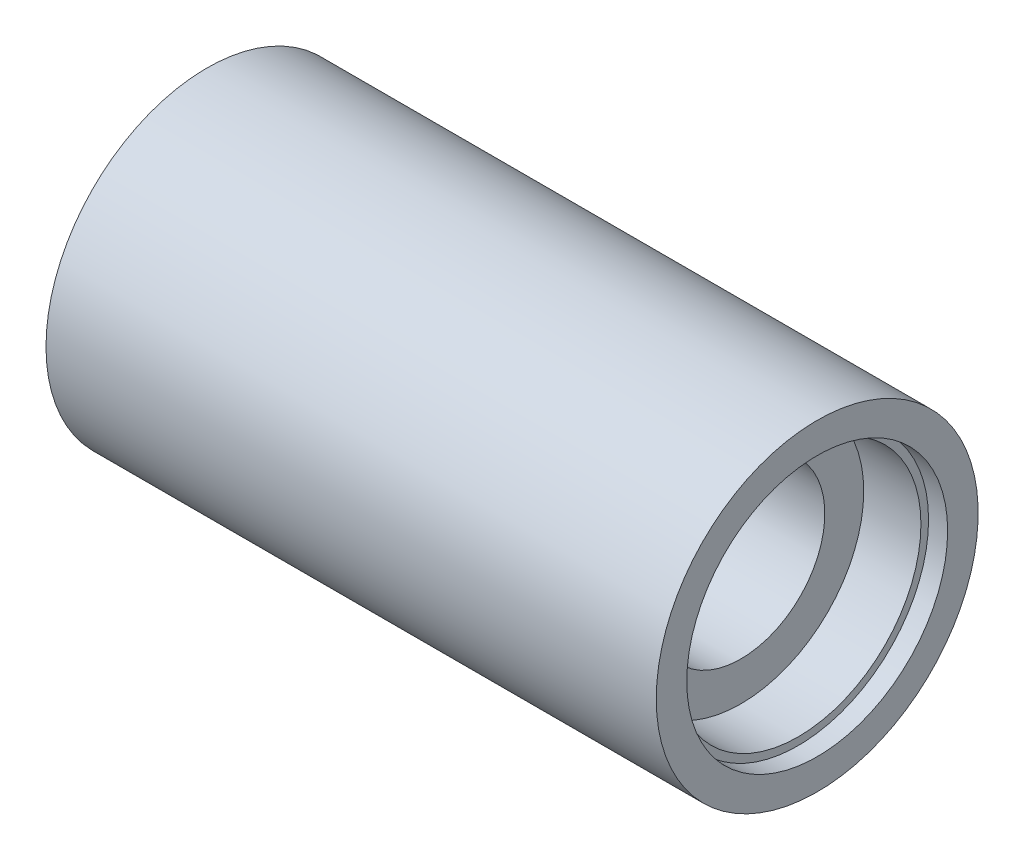
SolidWorks part; units mm, degrees
ref_plane "Front Plane" through (0, 0, 0) normal (0, 0, 1) x (1, 0, 0)
ref_plane "Top Plane" through (0, 0, 0) normal (0, 1, 0) x (1, 0, 0)
ref_plane "Right Plane" through (0, 0, 0) normal (1, 0, 0) x (0, 0, -1)
sketch "Sketch1" plane through (0, 0, 0) normal (0, 0, 1) x (1, 0, 0)
  line L0 (0, 0) -> (60.3235, 0) construction
  line L1 (0, 21.1) -> (40, 21.1)
  line L2 (40, 21.1) -> (40, 17.1)
  line L3 (40, 17.1) -> (37.5, 17.1)
  line L4 (37.5, 17.1) -> (37.5, 16.1)
  line L5 (37.5, 16.1) -> (30, 16.1)
  line L6 (30, 16.1) -> (30, 11)
  line L7 (30, 11) -> (0, 11)
  line L8 (0, 11) -> (0, 21.1)
  line L9 (0, 0) -> (0, 48.2132) construction
  dimension "D1" = 22
  dimension "D2" = 34.2
  dimension "D3" = 4
  dimension "D4" = 32.2
  dimension "D5" = 2.5
  dimension "D6" = 7.5
  dimension "D7" = 80
revolve "Revolve1" add sketch "Sketch1" angle 360 about L0
mirror "Mirror1" about plane through (0, 0, 0) normal (1, 0, 0) of "Revolve1"
